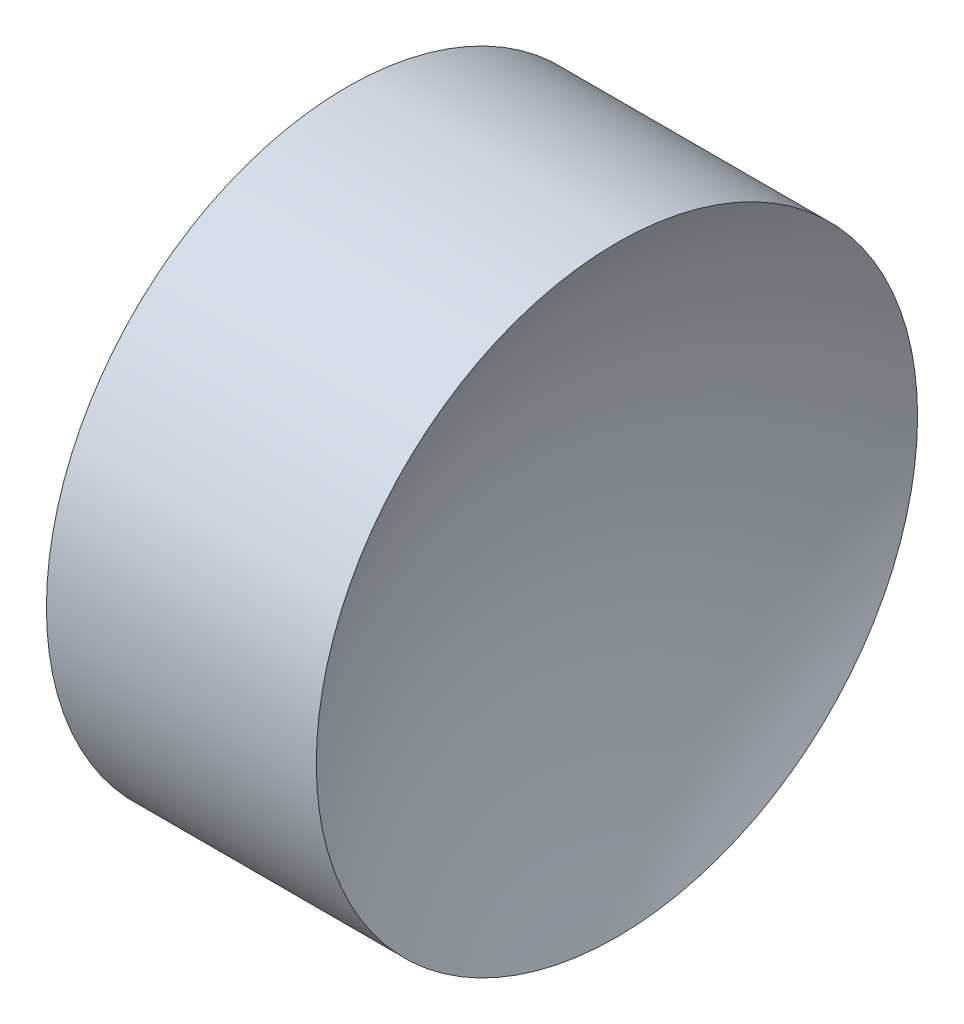
SolidWorks part; units mm, degrees
ref_plane "前视基准面" through (0, 0, 0) normal (0, 0, 1) x (1, 0, 0)
ref_plane "上视基准面" through (0, 0, 0) normal (0, 1, 0) x (1, 0, 0)
ref_plane "右视基准面" through (0, 0, 0) normal (1, 0, 0) x (0, 0, -1)
sketch "草图1" plane through (0, 0, 0) normal (0, 0, 1) x (1, 0, 0)
  line L0 (42.4499, 26.089) -> (55.6645, 26.089) construction
  line L1 (46.7952, 26.089) -> (49.2952, 26.089)
  line L3 (48.0452, 32.439) -> (50.8953, 32.439)
  line L4 (48.0452, 32.439) -> (45.1951, 32.439)
  arc A0 (46.7952, 26.089) -> (45.1951, 32.439) centre (33.3952, 26.089) ccw
  arc A1 (50.8953, 32.439) -> (49.2952, 26.089) centre (62.6952, 26.089) ccw
revolve "旋转1" add sketch "草图1" angle 360 about L0
